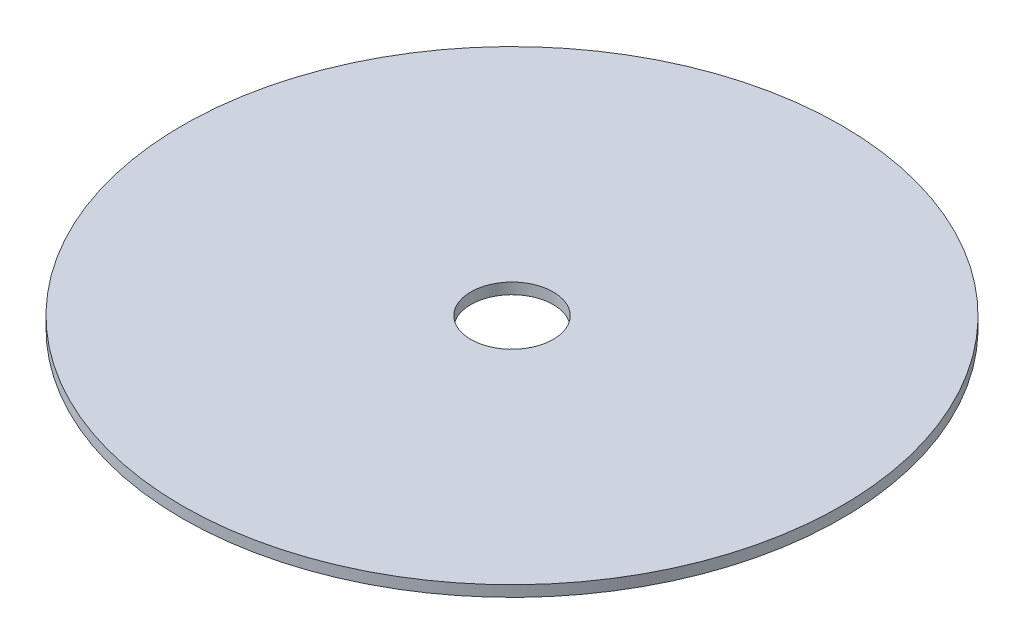
SolidWorks part; units mm, degrees
ref_plane "Face" through (0, 0, 0) normal (0, 0, 1) x (1, 0, 0)
ref_plane "Dessus" through (0, 0, 0) normal (0, 1, 0) x (1, 0, 0)
ref_plane "Droite" through (0, 0, 0) normal (1, 0, 0) x (0, 0, -1)
sketch "Esquisse1" plane through (0, 0, 0) normal (0, 1, 0) x (1, 0, 0)
  line L1 (0, 0) -> (18, 0)
  line L2 (0, 0) -> (0, 18)
  line L3 (0, 18) -> (18, 18)
  line L4 (18, 0) -> (18, 18)
  dimension "D1" = 18
  dimension "D2" = 18
extrude "Extrusion1" add sketch "Esquisse1" along normal blind 18
sketch "Esquisse2" plane through (0, 18, 0) normal (0, 1, 0) x (1, 0, 0)
  line L0 (9, 18) -> (9, -35.6055) construction
  line L1 (18, 18) -> (0, 18) construction
  line L2 (0, 0) -> (18, 0) construction
  circle A0 centre (9, -31.5) radius 60
  circle A1 centre (9, -31.5) radius 7.5
  dimension "D1" = 120
  dimension "D2" = 15
  dimension "D3" = 31.5
extrude "Extrusion2" add sketch "Esquisse2" along normal blind 2
